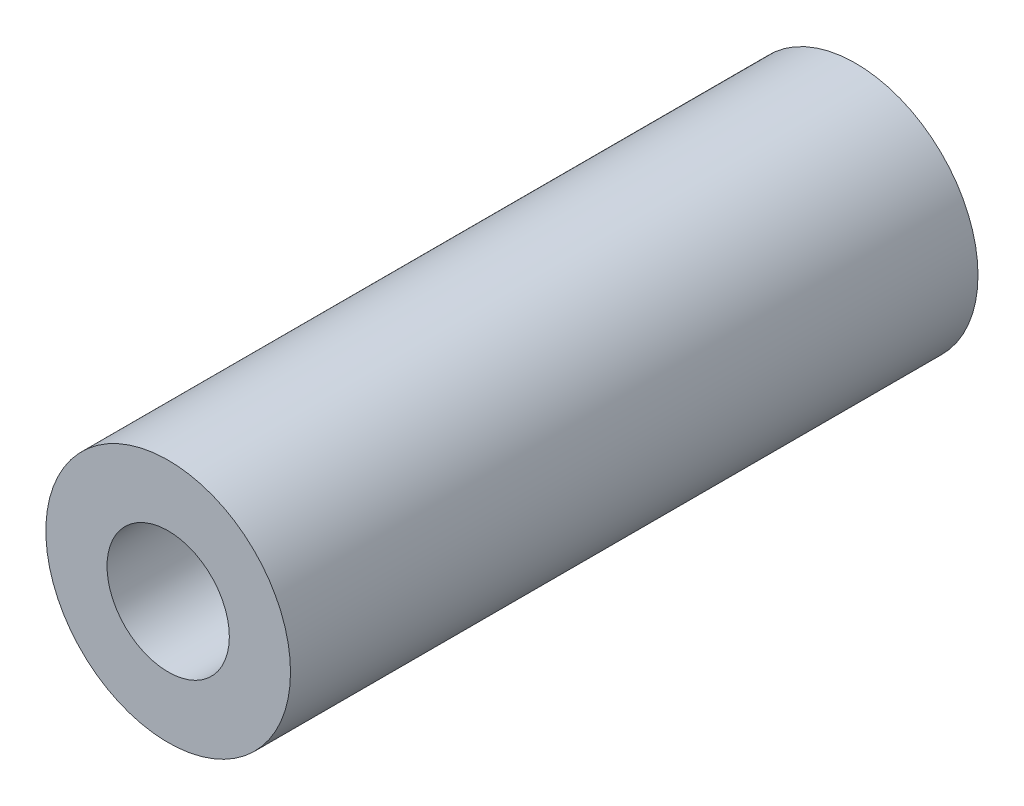
SolidWorks part; units mm, degrees
ref_plane "Front" through (0, 0, 0) normal (0, 0, 1) x (1, 0, 0)
ref_plane "Top" through (0, 0, 0) normal (0, 1, 0) x (1, 0, 0)
ref_plane "Right" through (0, 0, 0) normal (1, 0, 0) x (0, 0, -1)
sketch "Sketch1" plane through (0, 0, 0) normal (0, 0, 1) x (1, 0, 0)
  circle A0 centre (0, 0) radius 12.7
  circle A1 centre (0, 0) radius 6.35
  dimension "D1" = 25.4
  dimension "D2" = 6.35
extrude "Boss-Extrude1" add sketch "Sketch1" along normal blind 71.374
